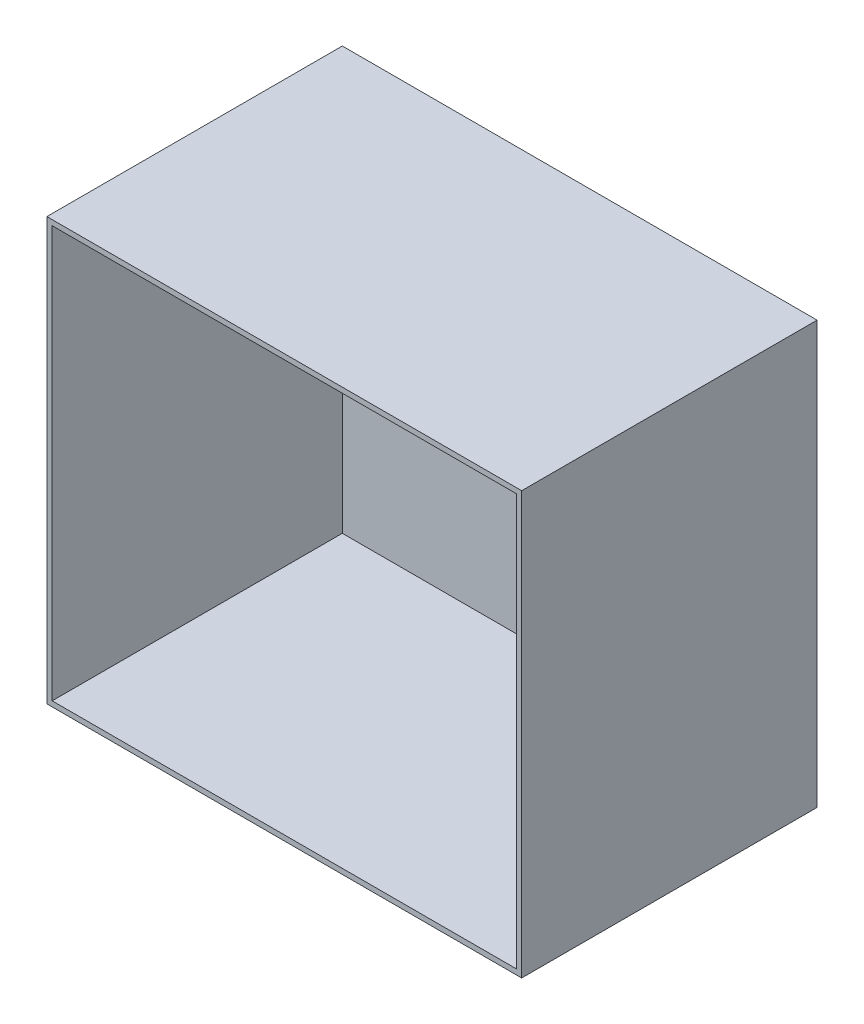
SolidWorks part; units mm, degrees
ref_plane "Front Plane" through (0, 0, 0) normal (0, 0, 1) x (1, 0, 0)
ref_plane "Top Plane" through (0, 0, 0) normal (0, 1, 0) x (1, 0, 0)
ref_plane "Right Plane" through (0, 0, 0) normal (1, 0, 0) x (0, 0, -1)
sketch "Sketch2" plane through (0, 0, 0) normal (0, 0, 1) x (1, 0, 0)
  line L1 (80, -80) -> (-80, -80)
  line L2 (80, -80) -> (80, 80)
  line L3 (80, 80) -> (-80, 80)
  line L4 (-80, -80) -> (-80, 80)
  line L5 (80, -80) -> (-80, 80) construction
  line L6 (80, 80) -> (-80, -80) construction
  point P0 (0, 0)
  dimension "D1" = 160
  dimension "D2" = 160
extrude "Boss-Extrude1" add sketch "Sketch2" along normal blind 2
sketch "Sketch3" plane through (0, -80, 0) normal (0, -1, 0) x (1, 0, 0)
  line L4 (-80, 0) -> (80, 0)
  line L5 (80, 0) -> (80, 2)
  line L6 (80, 2) -> (-80, 2)
  line L7 (-80, 2) -> (-80, 0)
  line L8 (-80, 0) -> (80, 0)
  line L9 (80, 0) -> (80, 2)
  line L10 (80, 2) -> (-80, 2)
  line L11 (-80, 2) -> (-80, 0)
  dimension "D1" = 0
sketch "Sketch4" plane through (80, 0, 0) normal (1, 0, 0) x (0, 0, -1)
  line L4 (0, -80) -> (0, 80)
  line L5 (0, 80) -> (-2, 80)
  line L6 (-2, 80) -> (-2, -80)
  line L7 (-2, -80) -> (0, -80)
  line L8 (0, -80) -> (0, 80)
  line L9 (0, 80) -> (-2, 80)
  line L10 (-2, 80) -> (-2, -80)
  line L11 (-2, -80) -> (0, -80)
  dimension "D1" = 0
extrude "Boss-Extrude3" add sketch "Sketch4" along normal blind 20
sketch "Sketch5" plane through (0, 0, 2) normal (0, 0, 1) x (1, 0, 0)
  line L0 (-80, -80) -> (100, -80)
  line L1 (100, -80) -> (100, 80)
  line L2 (100, 80) -> (-80, 80)
  line L3 (-80, 80) -> (-80, -80)
  line L5 (102, -82) -> (102, 82)
  line L6 (102, 82) -> (-82, 82)
  line L8 (-78, -78) -> (98, -78)
  line L9 (98, -78) -> (98, 78)
  line L10 (98, 78) -> (-78, 78)
  line L11 (-78, 78) -> (-78, -78)
  line L12 (-82, -82) -> (102, -82) construction
  line L13 (-82, 82) -> (-82, -82) construction
  line M2 (-80, 80) -> (-80, -80)
  line M3 (-80, -80) -> (100, -80)
  line M4 (100, -80) -> (100, 80)
  line M5 (100, 80) -> (-80, 80)
  dimension "D1" = 2
  dimension "D2" = 2
extrude "Boss-Extrude5" add sketch "Sketch5" along normal blind 100 contours L11 L10 L9 L8 M5 M2 M3 M4
sketch "Sketch6" plane through (0, 0, 102) normal (0, 0, 1) x (1, 0, 0)
  line L0 (98, -78) -> (98, 78) construction
  line L1 (98, -78) -> (98, 78)
  line L2 (-78, -78) -> (98, -78) construction
  line L3 (-78, -78) -> (98, -78)
  line L4 (100, 80) -> (-80, 80)
  line L5 (-80, 80) -> (-80, -80)
  line L6 (-80, -80) -> (100, -80)
  line L7 (100, -80) -> (100, 80)
  line L8 (100, 80) -> (-80, 80)
  line L9 (-80, 80) -> (-80, -80)
  line L10 (-80, -80) -> (100, -80)
  line L11 (100, -80) -> (100, 80)
  line L12 (-78, 78) -> (-78, -78) construction
  line L13 (98, 78) -> (-78, 78) construction
  line L14 (-78, 78) -> (-78, -78)
  line L15 (98, 78) -> (-78, 78)
  dimension "D1" = 0
extrude "Boss-Extrude6" add sketch "Sketch6" along normal blind 10
